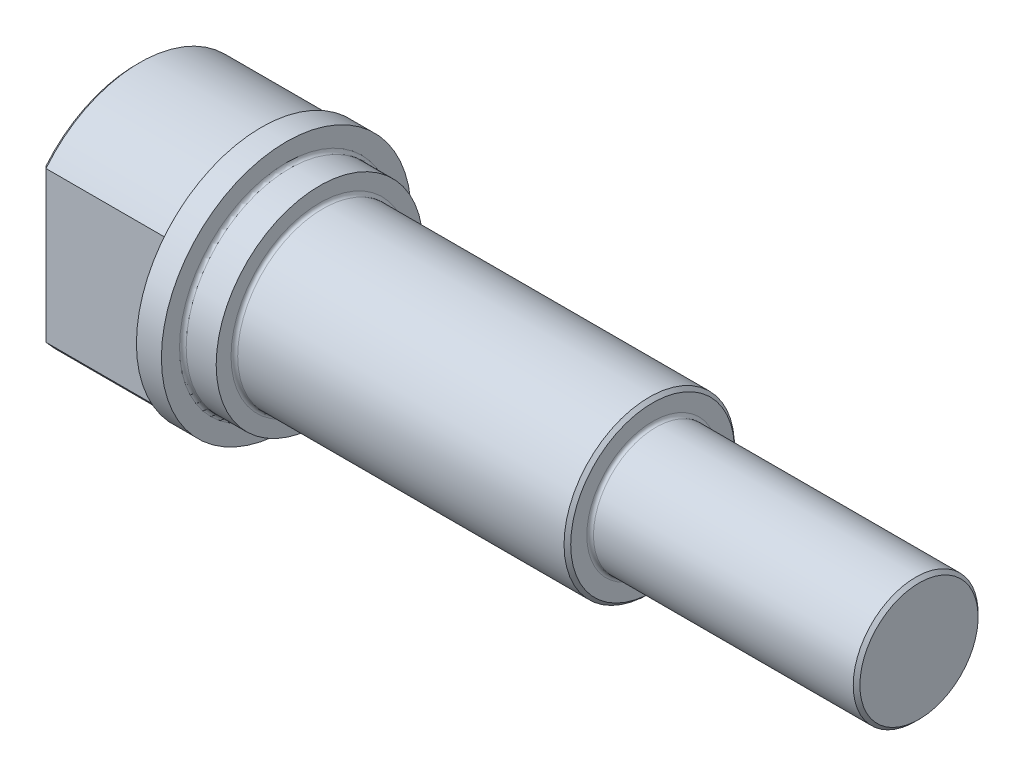
SolidWorks part; units mm, degrees
material "Plain Carbon Steel"
ref_plane "Front" through (0, 0, 0) normal (0, 0, 1) x (1, 0, 0)
ref_plane "Top" through (0, 0, 0) normal (0, 1, 0) x (1, 0, 0)
ref_plane "Right" through (0, 0, 0) normal (1, 0, 0) x (0, 0, -1)
sketch "Sketch1" plane through (0, 0, 0) normal (0, 0, 1) x (1, 0, 0)
  line L0 (0, 0) -> (123.964, 0) construction
  line L1 (0, 0) -> (0, 9.1694) construction
  line L2 (0, 9.1694) -> (9.525, 9.1694)
  line L3 (9.525, 9.1694) -> (9.525, 9.525)
  line L4 (9.525, 9.525) -> (11.43, 9.525)
  line L5 (11.43, 9.525) -> (11.43, 7.8867)
  line L6 (11.43, 7.8867) -> (13.97, 7.8867)
  line L7 (13.97, 7.8867) -> (13.97, 6.5)
  line L8 (13.97, 6.5) -> (39.37, 6.5)
  line L9 (39.37, 6.5) -> (39.37, 4.7625)
  line L10 (39.37, 4.7625) -> (59.69, 4.7625)
  line L11 (59.69, 4.7625) -> (59.69, 0)
  line L12 (0, 0) -> (59.69, 0) construction
  line L13 (0, 1.0999) -> (0.635, 0)
  line L14 (0, 1.0999) -> (0, 9.1694)
  line L15 (59.69, 0) -> (0.635, 0)
  dimension "D1" = 18.3388
  dimension "D2" = 9.525
  dimension "D3" = 15.7734
  dimension "D4" = 19.05
  dimension "D5" = 13
  dimension "D6" = 9.525
  dimension "D7" = 1.905
  dimension "D8" = 2.54
  dimension "D9" = 25.4
  dimension "D10" = 20.32
  dimension "D11" = 60
  dimension "D12" = 0.635
revolve "Revolve1" add sketch "Sketch1" angle 360 about L0
cosmetic thread "Cosmetic Thread1" parameters "D2"=8.2652
sketch "Sketch2" plane through (0, 0, 0) normal (-1, 0, 0) x (0, 0, 1)
  line L1 (-7.1501, -5.7406) -> (7.1501, -5.7406) construction
  line L2 (-7.1501, -5.7406) -> (-7.1501, 5.7406)
  line L3 (-7.1501, 5.7406) -> (7.1501, 5.7406) construction
  line L4 (7.1501, -5.7406) -> (7.1501, 5.7406)
  line L5 (-7.1501, -5.7406) -> (7.1501, 5.7406) construction
  line L6 (-7.1501, 5.7406) -> (7.1501, -5.7406) construction
  arc A1 (-7.1501, 5.7406) -> (-7.1501, -5.7406) centre (0, 0) ccw
  arc A2 (7.1501, -5.7406) -> (7.1501, 5.7406) centre (0, 0) ccw
  circle A3 centre (0, 0) radius 9.1694 construction
  dimension "D1" = 14.3002
extrude "Cut-Extrude1" cut sketch "Sketch2" against normal up to surface (9.525 mm away) up to face at (9.525, 0, 9.1694)
chamfer "Chamfer1" distance 0.254 angle 45 6 edges at (39.37, 0, 6.5) (59.69, 0, 4.7625) (0, 0, -7.1501) (0, 9.1694, 0) (0, -9.1694, 0) (0, 0, 7.1501)
fillet "Fillet1" radius 0.254 7 edges at (39.37, 0, 4.7625) (9.525, 9.1694, 0) (9.525, -9.1694, 0) (13.97, 0, 6.5) (11.43, 0, 7.8867) (9.525, 0, -7.1501) (9.525, 0, 7.1501)
